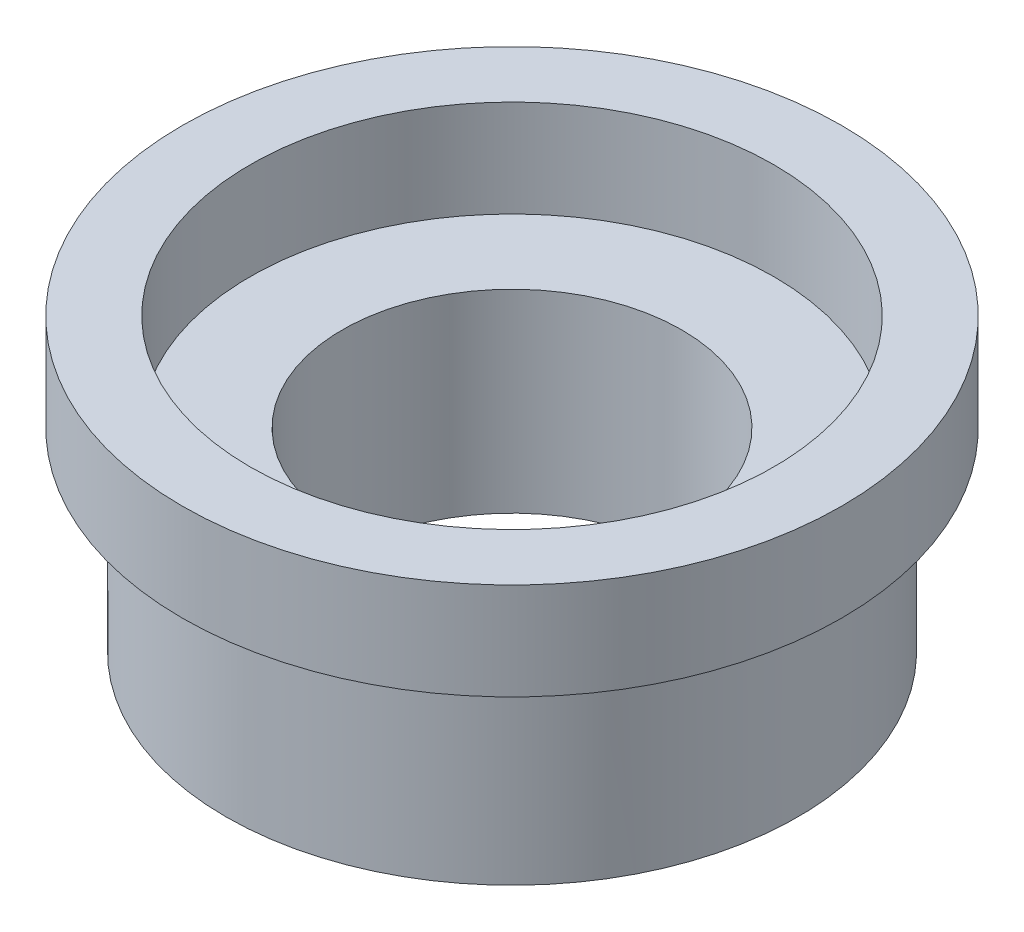
SolidWorks part; units mm, degrees
ref_plane "Front Plane" through (0, 0, 0) normal (0, 0, 1) x (1, 0, 0)
ref_plane "Top Plane" through (0, 0, 0) normal (0, 1, 0) x (1, 0, 0)
ref_plane "Right Plane" through (0, 0, 0) normal (1, 0, 0) x (0, 0, -1)
sketch "Sketch1" plane through (0, 0, 0) normal (0, 1, 0) x (1, 0, 0)
  circle A0 centre (0, 0) radius 43.18
  circle A1 centre (0, 0) radius 34.29
  dimension "D1" = 86.36
  dimension "D2" = 68.58
extrude "Boss-Extrude1" add sketch "Sketch1" along normal blind 12.7
sketch "Sketch2" plane through (0, 0, 0) normal (0, -1, 0) x (1, 0, 0)
  circle A0 centre (0, 0) radius 37.465
  circle A1 centre (0, 0) radius 22.225
  dimension "D1" = 74.93
  dimension "D2" = 44.45
extrude "Boss-Extrude2" add sketch "Sketch2" along normal blind 25.4
